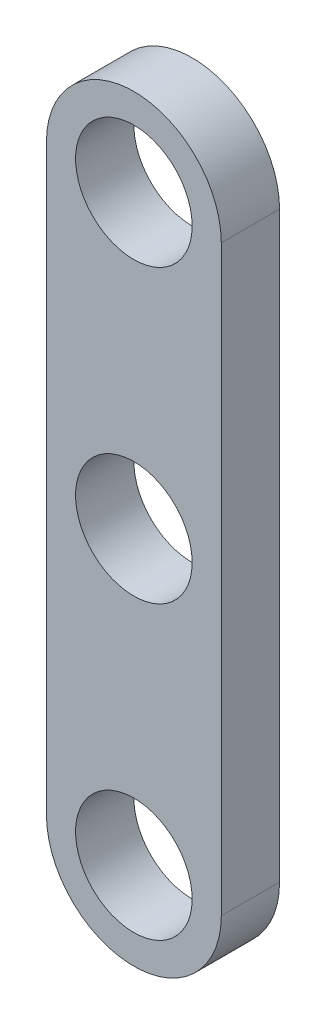
SolidWorks part; units mm, degrees
ref_plane "Front Plane" through (0, 0, 0) normal (0, 0, 1) x (1, 0, 0)
ref_plane "Top Plane" through (0, 0, 0) normal (0, 1, 0) x (1, 0, 0)
ref_plane "Right Plane" through (0, 0, 0) normal (1, 0, 0) x (0, 0, -1)
sketch "Sketch1" plane through (0, 0, 0) normal (0, 0, 1) x (1, 0, 0)
  line L0 (0, 0) -> (0, 50) construction
  line L1 (-7.5, 0) -> (-7.5, 50)
  line L2 (7.5, 0) -> (7.5, 50)
  arc A0 (-7.5, 0) -> (7.5, 0) centre (0, 0) ccw
  arc A1 (7.5, 50) -> (-7.5, 50) centre (0, 50) ccw
  circle A2 centre (0, 50) radius 5
  circle A3 centre (0, 25) radius 5
  circle A4 centre (0, 0) radius 5
  point P3 (0, 25)
  dimension "D1" = 10
  dimension "D2" = 25
  dimension "D3" = 15
extrude "Boss-Extrude1" add sketch "Sketch1" along normal mid plane 5
scale "Scale1" bodies to scale 101 scale about centroid uniform scaling yes scale factor 0.3
